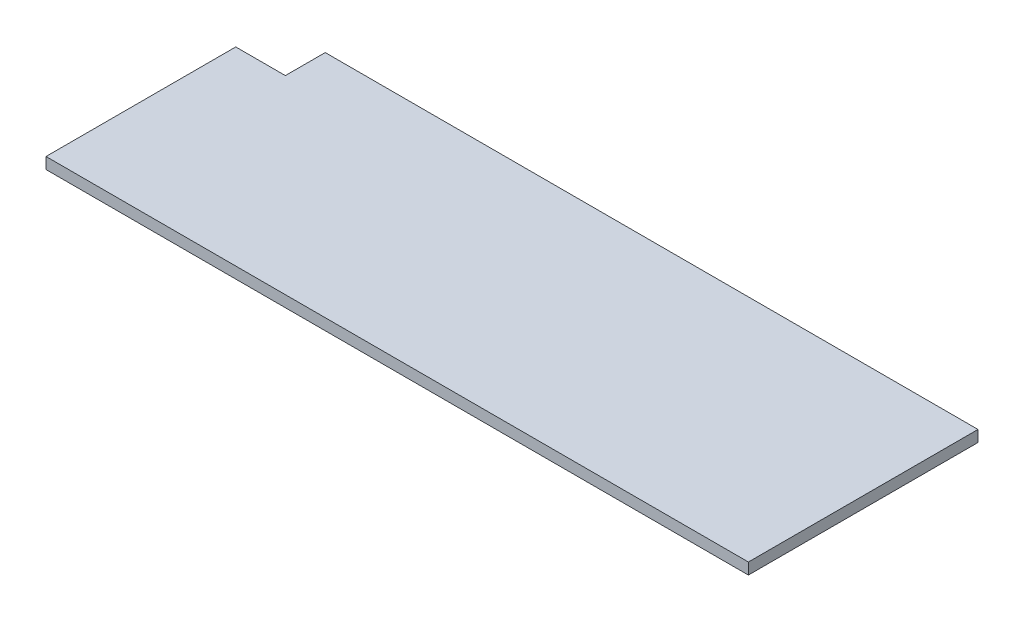
SolidWorks part; units mm, degrees
ref_plane "Front Plane" through (0, 0, 0) normal (0, 0, 1) x (1, 0, 0)
ref_plane "Top Plane" through (0, 0, 0) normal (0, 1, 0) x (1, 0, 0)
ref_plane "Right Plane" through (0, 0, 0) normal (1, 0, 0) x (0, 0, -1)
sketch "Sketch1" plane through (0, 0, 0) normal (0, 1, 0) x (1, 0, 0)
  line L0 (0, 0) -> (0, 44.75)
  line L1 (0, 44.75) -> (11.7, 44.75)
  line L2 (11.7, 44.75) -> (11.7, 54.15)
  line L3 (11.7, 54.15) -> (165.65, 54.15)
  line L6 (165.65, 54.15) -> (165.65, 0)
  line L13 (165.65, 0) -> (0, 0)
  dimension "D2" = 165.65
  dimension "D3" = 9.4
  dimension "D9" = 11.7
  dimension "D11" = 54.15
extrude "Boss-Extrude1" add sketch "Sketch1" along normal blind 2.67
